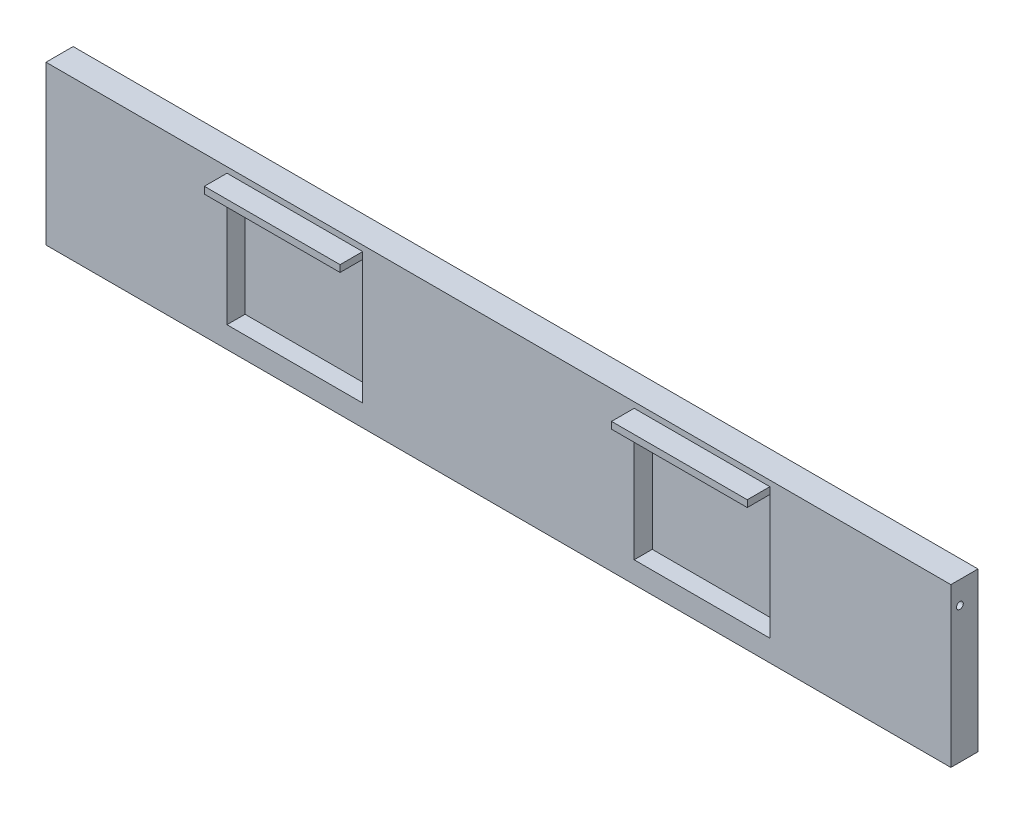
SolidWorks part; units mm, degrees
material "Pine"
ref_plane "Front Plane" through (0, 0, 0) normal (0, 0, 1) x (1, 0, 0)
ref_plane "Top Plane" through (0, 0, 0) normal (0, 1, 0) x (1, 0, 0)
ref_plane "Right Plane" through (0, 0, 0) normal (1, 0, 0) x (0, 0, -1)
sketch "Sketch1" plane through (0, 0, 0) normal (0, 0, 1) x (1, 0, 0)
  line L1 (-200, -35) -> (200, -35)
  line L2 (-200, -35) -> (-200, 35)
  line L3 (-200, 35) -> (200, 35)
  line L4 (200, -35) -> (200, 35)
  line L5 (-200, -35) -> (200, 35) construction
  line L6 (-200, 35) -> (200, -35) construction
  point P0 (0, 0)
  dimension "D1" = 400
  dimension "D2" = 70
extrude "Boss-Extrude1" add sketch "Sketch1" along normal blind 12
sketch "Sketch3" plane through (0, 0, 12) normal (0, 0, 1) x (1, 0, 0)
  line L0 (-200, 35) -> (-200, -35) construction
  line L1 (-60, 29.5) -> (60, 29.5) construction
  line L2 (-60, 29.5) -> (-60, 20.5) construction
  line L3 (-60, 20.5) -> (60, 20.5) construction
  line L4 (60, 29.5) -> (60, 20.5) construction
  line L5 (-60, 29.5) -> (60, 20.5) construction
  line L6 (-60, 20.5) -> (60, 29.5) construction
  line L7 (200, 35) -> (-200, 35) construction
  line L8 (0, 29.5) -> (0, 20.5) construction
  line L17 (-60, -25.5) -> (-120, -25.5)
  line L18 (60, 29.5) -> (120, 29.5)
  line L19 (60, 29.5) -> (60, -25.5)
  line L20 (60, -25.5) -> (120, -25.5)
  line L21 (120, 29.5) -> (120, -25.5)
  line L22 (-120, 29.5) -> (-120, -25.5)
  line L23 (-60, 29.5) -> (-120, 29.5)
  line L24 (-60, 29.5) -> (-60, -25.5)
  point P0 (0, 25)
  dimension "D1" = 120
  dimension "D2" = 200
  dimension "D3" = 9
  dimension "D4" = 10
  dimension "D5" = 55
  dimension "D6" = 60
extrude "Cut-Extrude1" cut sketch "Sketch3" against normal blind 8
sketch "Sketch4" plane through (-200, 0, 0) normal (-1, 0, 0) x (0, 0, 1)
  line L0 (12, 35) -> (0, 35) construction
  line L1 (12, 35) -> (12, -35) construction
  circle A0 centre (8, 25) radius 1.5
  dimension "D1" = 3
  dimension "D2" = 10
  dimension "D3" = 4
extrude "Cut-Extrude2" cut sketch "Sketch4" against normal through all
sketch "Sketch5" plane through (0, 0, 12) normal (0, 0, 1) x (1, 0, 0)
  line L0 (0, 35) -> (0, -35) construction
  line L1 (200, 35) -> (-200, 35) construction
  line L2 (-200, -35) -> (200, -35) construction
  line L3 (-120, 29.5) -> (-60, 29.5)
  line L4 (-120, 29.5) -> (-120, 32.5)
  line L5 (-60, 29.5) -> (-60, 32.5)
  line L6 (-120, 32.5) -> (-60, 32.5)
  line L7 (60, 29.5) -> (60, 32.5)
  line L8 (120, 32.5) -> (60, 32.5)
  line L9 (120, 29.5) -> (120, 32.5)
  line L10 (120, 29.5) -> (60, 29.5)
  dimension "D1" = 3
extrude "Boss-Extrude2" add sketch "Sketch5" along normal blind 10
sketch "Sketch6" plane through (0, 0, 0) normal (0, 0, -1) x (-1, 0, 0)
  line L0 (0, 35) -> (0, -35) construction
  line L1 (-200, 35) -> (200, 35) construction
  line L2 (200, -35) -> (-200, -35) construction
  line L3 (-200, -35) -> (-200, 35) construction
  point P0 (-185, 0)
  point P1 (-175, 5)
  point P10 (-175, -5)
  point P11 (175, -5)
  point P12 (175, 5)
  point P13 (185, 0)
  dimension "D1" = 15
  dimension "D2" = 10
  dimension "D3" = 25
  dimension "D4" = 30
  dimension "D5" = 35
  dimension "D6" = 25
